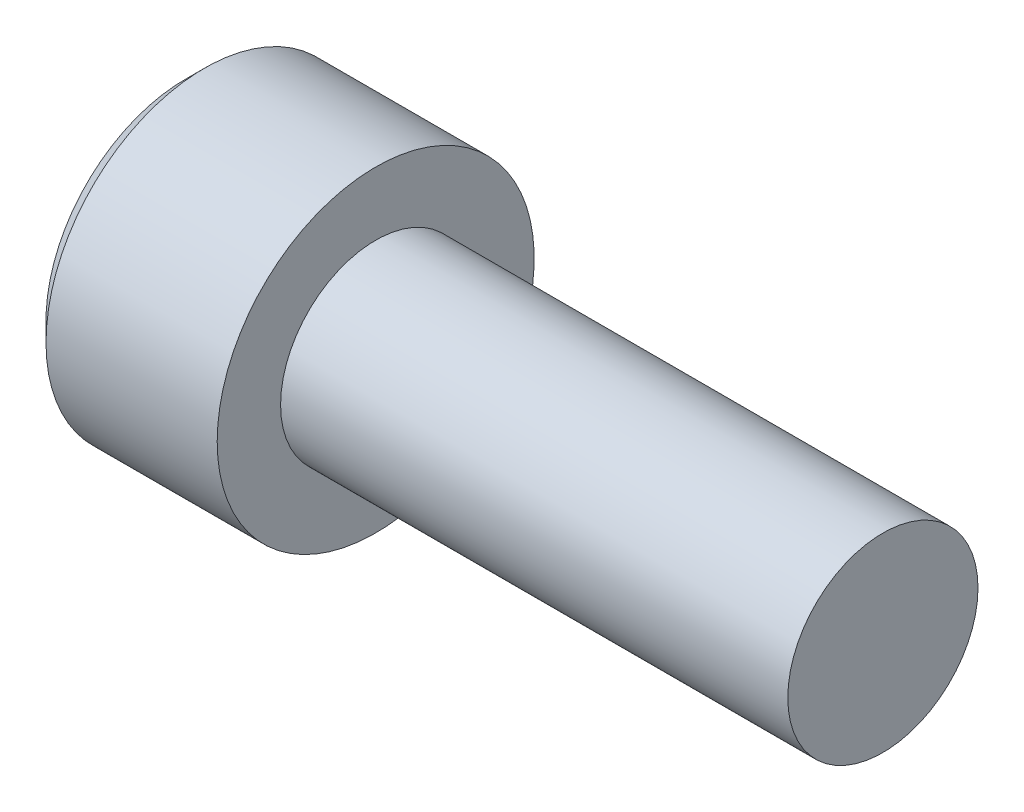
SolidWorks part; units mm, degrees
material "相当于SUS304"
ref_plane "Front Plane" through (0, 0, 0) normal (0, 0, 1) x (1, 0, 0)
ref_plane "Top Plane" through (0, 0, 0) normal (0, 1, 0) x (1, 0, 0)
ref_plane "Right Plane" through (0, 0, 0) normal (1, 0, 0) x (0, 0, -1)
sketch "Sketch1" plane through (0, 0, 0) normal (0, 0, 1) x (1, 0, 0)
  line L0 (-6, 0) -> (16, 0) construction
  line L1 (0, 3) -> (16, 3)
  line L3 (-6, 0) -> (16, 0)
  line L4 (16, 3) -> (16, 0)
  line L6 (0, 3) -> (0, 5)
  line L7 (0, 5) -> (-6, 5)
  line L8 (-6, 0) -> (-6, 5)
  dimension "L" = 16
  dimension "M" = 6
  dimension "E" = 6
  dimension "A" = 10
revolve "Revolve1" add sketch "Sketch1" about L0
cosmetic thread "Thread1" parameters "L_s"=10, "ATD"=4.917
sketch "Sketch2" plane through (0, 0, 0) normal (0, 0, 1) x (1, 0, 0)
  line L0 (-6, 0) -> (-1.4978, 0) construction
  line L1 (-6, 0) -> (16, 0) construction
  line L2 (-1.4978, 0) -> (-3, 2.5)
  line L3 (-3, 2.5) -> (-6, 2.5)
  line L4 (-6, 0) -> (-6, 5) construction
  line L5 (-6, 2.5) -> (-6, 0)
  line L6 (-6, 0) -> (-1.4978, 0)
  dimension "MSM_1" = 3
  dimension "FIX_2" = 59
revolve "Cut-Revolve1" cut sketch "Sketch2" about L0
sketch "Sketch3" plane through (-6, 0, 0) normal (-1, 0, 0) x (0, 0, 1)
  line L0 (0, -5.5) -> (0, 5.5) construction
  line L1 (2.5, 1.4434) -> (0, 2.8868)
  line L2 (0, 2.8868) -> (-2.5, 1.4434)
  line L3 (-2.5, 1.4434) -> (-2.5, -1.4434)
  line L4 (-2.5, -1.4434) -> (0, -2.8868)
  line L5 (0, -2.8868) -> (2.5, -1.4434)
  line L6 (2.5, -1.4434) -> (2.5, 1.4434)
  circle A0 centre (0, 0) radius 2.5 construction
extrude "Cut-Extrude1" cut sketch "Sketch3" against normal blind 3
chamfer "Chamfer1" distance 0.6 1 edges at (-6, 0, 5)
